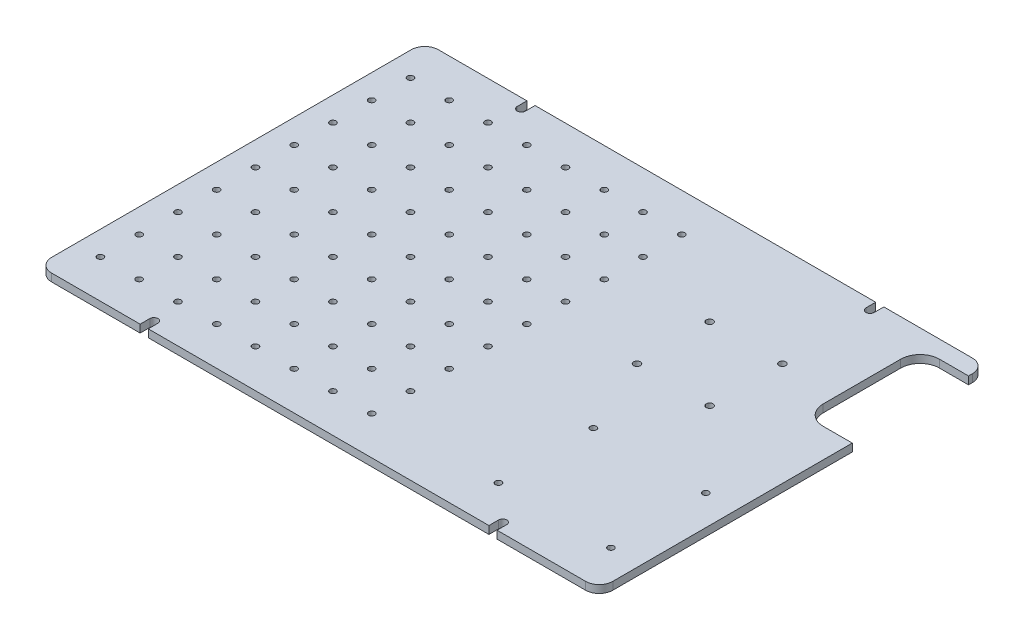
SolidWorks part; units mm, degrees
ref_plane "Front Plane" through (0, 0, 0) normal (0, 0, 1) x (1, 0, 0)
ref_plane "Top Plane" through (0, 0, 0) normal (0, 1, 0) x (1, 0, 0)
ref_plane "Right Plane" through (0, 0, 0) normal (1, 0, 0) x (0, 0, -1)
sketch "Sketch1" plane through (0, 0, 0) normal (0, 1, 0) x (1, 0, 0)
  line L1 (-144.8, 99.8) -> (144.8, 99.8)
  line L2 (-144.8, 99.8) -> (-144.8, -99.8)
  line L3 (-144.8, -99.8) -> (144.8, -99.8)
  line L4 (144.8, 99.8) -> (144.8, -99.8)
  line L5 (-144.8, 99.8) -> (144.8, -99.8) construction
  line L6 (-144.8, -99.8) -> (144.8, 99.8) construction
  point P0 (0, 0)
  dimension "D1" = 289.6
  dimension "D2" = 199.6
extrude "Boss-Extrude1" add sketch "Sketch1" along normal blind 4
sketch "Sketch2" plane through (0, 4, 0) normal (0, 1, 0) x (1, 0, 0)
  line L0 (-90, 104.8) -> (-90, 94.8) construction
  line L1 (-87.9, 104.8) -> (-87.9, 94.8)
  line L2 (-92.1, 104.8) -> (-92.1, 94.8)
  line L3 (90, 104.8) -> (90, 94.8) construction
  line L4 (92.1, 104.8) -> (92.1, 94.8)
  line L5 (87.9, 104.8) -> (87.9, 94.8)
  line L6 (144.8, 99.8) -> (-144.8, 99.8) construction
  arc A0 (-87.9, 104.8) -> (-92.1, 104.8) centre (-90, 104.8) ccw
  arc A1 (-92.1, 94.8) -> (-87.9, 94.8) centre (-90, 94.8) ccw
  arc A2 (92.1, 104.8) -> (87.9, 104.8) centre (90, 104.8) ccw
  arc A3 (87.9, 94.8) -> (92.1, 94.8) centre (90, 94.8) ccw
  point P2 (-90, 99.8)
  point P7 (90, 99.8)
  dimension "D1" = 4.2
  dimension "D2" = 180
  dimension "D3" = 10
  dimension "D4" = 90
extrude "Cut-Extrude1" cut sketch "Sketch2" against normal through all
mirror "Mirror1" about plane through (0, 0, 0) normal (0, 0, 1) of "Cut-Extrude1"
fillet "Fillet1" radius 7 4 edges at (144.8, 2, -99.8) (144.8, 2, 99.8) (-144.8, 2, 99.8) (-144.8, 2, -99.8)
sketch "Sketch3" plane through (0, 4, 0) normal (0, 1, 0) x (1, 0, 0)
  line L0 (144.8, -92.8) -> (144.8, 92.8) construction
  line L1 (119.8, 90.8) -> (144.8, 90.8)
  line L2 (119.8, 90.8) -> (119.8, 30.8)
  line L3 (119.8, 30.8) -> (144.8, 30.8)
  line L4 (144.8, 90.8) -> (144.8, 30.8)
  line L6 (137.8, 99.8) -> (92.1, 99.8) construction
  dimension "D1" = 25
  dimension "D2" = 60
  dimension "D3" = 9
extrude "Cut-Extrude2" cut sketch "Sketch3" against normal through all
fillet "Fillet2" radius 10 2 edges at (119.8, 2, -30.8) (119.8, 2, -90.8)
sketch "Sketch4" plane through (0, 4, 0) normal (0, 1, 0) x (1, 0, 0)
  line L1 (144.8, -92.8) -> (144.8, 30.8) construction
  line L2 (-87.9, -99.8) -> (87.9, -99.8) construction
  line B0 (132.8, -81.8) -> (132.8, -25.8) construction
  line B1 (45.428, -81.8) -> (132.8, -81.8) construction
  circle B2 centre (129.3, -78.3) radius 1.6
  circle B3 centre (71.3, -78.3) radius 1.6
  circle B4 centre (129.3, -29.3) radius 1.6
  circle B5 centre (71.3, -29.3) radius 1.6
  dimension "D1" = 12
  dimension "D2" = 18
sketch_block_instance "Raspberry_Pi_3-1"
sketch_block "Raspberry_Pi_3" parameters "D11"=3.2, "D1"=87.372, "D2"=56, "D3"=3.5, "D4"=3.5, "D5"=3.5, "D6"=3.5, "D7"=3.5, "D8"=3.5, "D9"=58, "D10"=58
extrude "Cut-Extrude3" cut sketch "Sketch4" against normal through all
sketch "Sketch5" plane through (0, 4, 0) normal (0, 1, 0) x (1, 0, 0)
  circle A0 centre (91.3, 10.7) radius 1.75
  circle A1 centre (91.3, 48.2) radius 1.75
  circle A2 centre (53.8, 48.2) radius 1.75
  circle A3 centre (53.8, 10.7) radius 1.75
  circle A4 centre (71.3, -29.3) radius 1.6 construction
  dimension "D3" = 3.5
  dimension "D1" = 37.5
  dimension "D2" = 37.5
  dimension "D4" = 40
  dimension "D5" = 20
extrude "Cut-Extrude4" cut sketch "Sketch5" against normal through all
sketch "Sketch6" plane through (0, 4, 0) normal (0, 1, 0) x (1, 0, 0)
  line L1 (87.9, 99.8) -> (-87.9, 99.8) construction
  line L4 (-144.8, 92.8) -> (-144.8, -92.8) construction
  circle A0 centre (7.6, 80) radius 1.59
  circle A1 centre (-12.4, 80) radius 1.59
  circle A2 centre (-32.4, 80) radius 1.59
  circle A3 centre (-52.4, 80) radius 1.59
  circle A4 centre (-72.4, 80) radius 1.59
  circle A5 centre (-92.4, 80) radius 1.59
  circle A6 centre (-112.4, 80) radius 1.59
  circle A7 centre (-12.4, 60) radius 1.59
  circle A8 centre (-32.4, 60) radius 1.59
  circle A9 centre (-52.4, 60) radius 1.59
  circle A10 centre (-72.4, 60) radius 1.59
  circle A11 centre (-92.4, 60) radius 1.59
  circle A12 centre (-112.4, 60) radius 1.59
  circle A13 centre (-12.4, 40) radius 1.59
  circle A14 centre (-32.4, 40) radius 1.59
  circle A15 centre (-52.4, 40) radius 1.59
  circle A16 centre (-72.4, 40) radius 1.59
  circle A17 centre (-92.4, 40) radius 1.59
  circle A18 centre (-112.4, 40) radius 1.59
  circle A19 centre (-12.4, 20) radius 1.59
  circle A20 centre (-32.4, 20) radius 1.59
  circle A21 centre (-52.4, 20) radius 1.59
  circle A22 centre (-72.4, 20) radius 1.59
  circle A23 centre (-92.4, 20) radius 1.59
  circle A24 centre (-112.4, 20) radius 1.59
  circle A25 centre (-12.4, 0) radius 1.59
  circle A26 centre (-32.4, 0) radius 1.59
  circle A27 centre (-52.4, 0) radius 1.59
  circle A28 centre (-72.4, 0) radius 1.59
  circle A29 centre (-92.4, 0) radius 1.59
  circle A30 centre (-112.4, 0) radius 1.59
  circle A31 centre (-12.4, -20) radius 1.59
  circle A32 centre (-32.4, -20) radius 1.59
  circle A33 centre (-52.4, -20) radius 1.59
  circle A34 centre (-72.4, -20) radius 1.59
  circle A35 centre (-92.4, -20) radius 1.59
  circle A36 centre (-112.4, -20) radius 1.59
  circle A37 centre (-12.4, -40) radius 1.59
  circle A38 centre (-32.4, -40) radius 1.59
  circle A39 centre (-52.4, -40) radius 1.59
  circle A40 centre (-72.4, -40) radius 1.59
  circle A41 centre (-92.4, -40) radius 1.59
  circle A42 centre (-112.4, -40) radius 1.59
  circle A43 centre (-12.4, -60) radius 1.59
  circle A44 centre (-32.4, -60) radius 1.59
  circle A45 centre (-52.4, -60) radius 1.59
  circle A46 centre (-72.4, -60) radius 1.59
  circle A47 centre (-92.4, -60) radius 1.59
  circle A48 centre (-112.4, -60) radius 1.59
  circle A49 centre (-12.4, -80) radius 1.59
  circle A50 centre (-32.4, -80) radius 1.59
  circle A51 centre (-52.4, -80) radius 1.59
  circle A52 centre (-72.4, -80) radius 1.59
  circle A53 centre (-92.4, -80) radius 1.59
  circle A54 centre (-112.4, -80) radius 1.59
  circle A55 centre (7.6, 60) radius 1.59
  circle A56 centre (7.6, 40) radius 1.59
  circle A57 centre (7.6, 20) radius 1.59
  circle A58 centre (7.6, 0) radius 1.59
  circle A59 centre (7.6, -20) radius 1.59
  circle A60 centre (7.6, -40) radius 1.59
  circle A61 centre (7.6, -60) radius 1.59
  circle A62 centre (7.6, -80) radius 1.59
  circle A63 centre (-132.4, 80) radius 1.59
  circle A64 centre (-132.4, 60) radius 1.59
  circle A65 centre (-132.4, 40) radius 1.59
  circle A66 centre (-132.4, 20) radius 1.59
  circle A67 centre (-132.4, 0) radius 1.59
  circle A68 centre (-132.4, -20) radius 1.59
  circle A69 centre (-132.4, -40) radius 1.59
  circle A70 centre (-132.4, -60) radius 1.59
  circle A71 centre (-132.4, -80) radius 1.59
  dimension "D2" = 3.18
  dimension "D1" = 19.8
  dimension "D5" = 92.4
  dimension "D3" = 8
  dimension "D4" = 9
extrude "Cut-Extrude5" cut sketch "Sketch6" against normal through all
